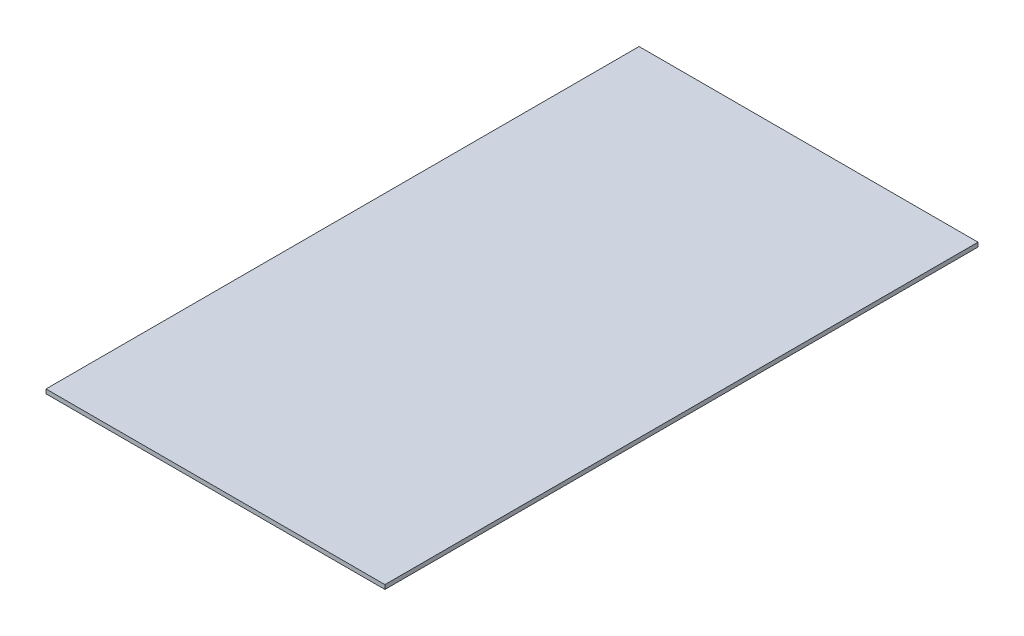
SolidWorks part; units mm, degrees
ref_plane "Front Plane" through (0, 0, 0) normal (0, 0, 1) x (1, 0, 0)
ref_plane "Top Plane" through (0, 0, 0) normal (0, 1, 0) x (1, 0, 0)
ref_plane "Right Plane" through (0, 0, 0) normal (1, 0, 0) x (0, 0, -1)
sketch "Sketch1" plane through (0, 0, 0) normal (0, 1, 0) x (1, 0, 0)
  line L0 (-200, 350) -> (200, -350) construction
  line L1 (-200, 350) -> (200, 350)
  line L2 (-200, 350) -> (-200, -350)
  line L3 (-200, -350) -> (200, -350)
  line L4 (200, 350) -> (200, -350)
  line L5 (200, 350) -> (-200, -350) construction
  dimension "D1" = 700
  dimension "D2" = 400
extrude "Boss-Extrude1" add sketch "Sketch1" along normal blind 5
